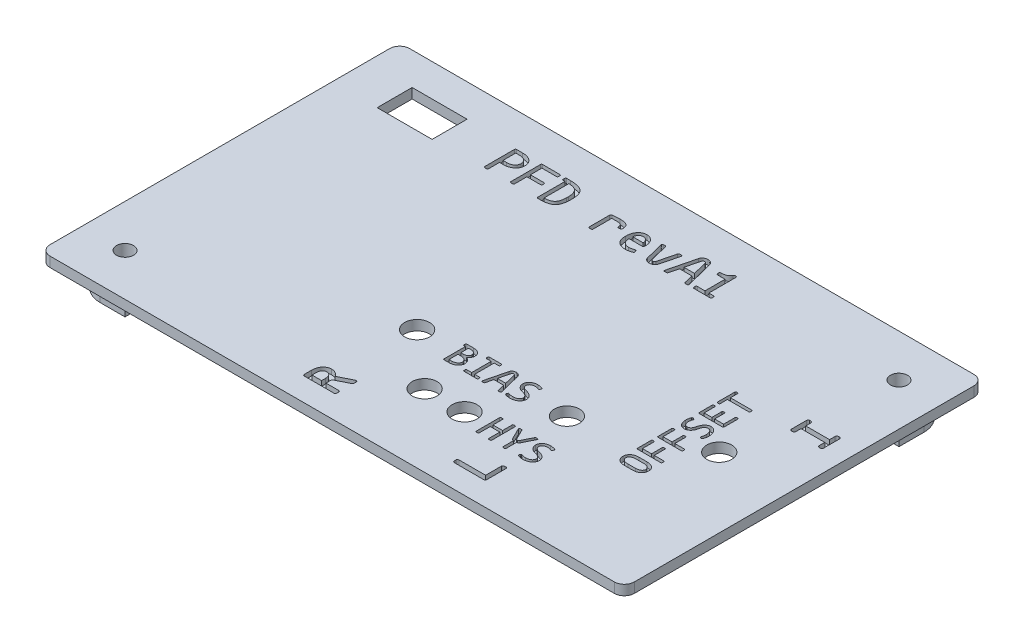
SolidWorks part; units mm, degrees
ref_plane "Front" through (0, 0, 0) normal (0, 0, 1) x (1, 0, 0)
ref_plane "Top" through (0, 0, 0) normal (0, 1, 0) x (1, 0, 0)
ref_plane "Right" through (0, 0, 0) normal (1, 0, 0) x (0, 0, -1)
sketch "Sketch1" plane through (0, 5.45, 0) normal (0, 1, 0) x (1, 0, 0)
  line L1 (-0.502, 5.4133) -> (4.498, 5.4133)
  line L2 (-5.502, 10.4133) -> (-5.502, 15.4133)
  line L3 (-5.502, 15.4133) -> (-0.502, 15.4133)
  line L4 (4.498, 5.4133) -> (4.498, 10.4133)
  line L5 (99.498, 70.4133) -> (94.498, 70.4133)
  line L6 (104.498, 65.4133) -> (104.498, 60.4133)
  line L7 (104.498, 60.4133) -> (99.498, 60.4133)
  line L8 (94.498, 70.4133) -> (94.498, 65.4133)
  arc A0 (99.498, 70.4133) -> (104.498, 65.4133) centre (99.498, 65.4133) cw
  arc A1 (-0.502, 5.4133) -> (-5.502, 10.4133) centre (-0.502, 10.4133) cw
  arc A2 (99.498, 60.4133) -> (94.498, 65.4133) centre (99.498, 65.4133) cw
  arc A3 (-0.502, 15.4133) -> (4.498, 10.4133) centre (-0.502, 10.4133) cw
  point P12 (104.498, 70.4133)
  point P15 (-5.502, 5.4133)
  point P18 (94.498, 60.4133)
  point P21 (4.498, 15.4133)
  dimension "D5" = 5
  dimension "D1" = 10
  dimension "D2" = 10
  dimension "D3" = 10
  dimension "D4" = 10
extrude "Boss-Extrude1" add sketch "Sketch1" along normal up to surface (4.55 mm away)
sketch "Sketch2" plane through (0, 10, 0) normal (0, 1, 0) x (1, 0, 0)
  line L0 (-7.002, 73.9133) -> (105.998, 73.9133) construction
  line L1 (-9.002, 1.9133) -> (107.998, 1.9133)
  line L2 (-9.002, 1.9133) -> (-9.002, 73.9133)
  line L3 (-9.002, 73.9133) -> (107.998, 73.9133)
  line L4 (107.998, 1.9133) -> (107.998, 73.9133)
  line L5 (107.998, 52.9133) -> (107.998, 71.9133) construction
  line L6 (-7.002, 1.9133) -> (37.498, 1.9133) construction
  line L7 (-9.002, 3.9133) -> (-9.002, 71.9133) construction
extrude "Boss-Extrude2" add sketch "Sketch2" along normal blind 2
fillet "Fillet1" radius 2 4 edges at (-9.002, 11, -1.9133) (-9.002, 11, -73.9133) (107.998, 11, -1.9133) (107.998, 11, -73.9133)
sketch "Sketch3" plane through (0, 12, 0) normal (0, 1, 0) x (1, 0, 0)
  line L0 (-7.002, 1.9133) -> (105.998, 1.9133) construction
  line L1 (104.498, 5.4133) -> (-5.502, 5.4133) construction
  line L2 (104.498, 5.4133) -> (104.498, 70.4133) construction
  line L3 (104.498, 70.4133) -> (-5.502, 70.4133) construction
  line L4 (-5.502, 5.4133) -> (-5.502, 70.4133) construction
  line L5 (107.998, 3.9133) -> (107.998, 71.9133) construction
  line L7 (10.998, 60.4133) -> (-0.002, 60.4133)
  line L8 (10.998, 60.4133) -> (10.998, 67.4133)
  line L9 (10.998, 67.4133) -> (-0.002, 67.4133)
  line L10 (-0.002, 60.4133) -> (-0.002, 67.4133)
  circle A0 centre (72.498, 25.9133) radius 2.5
  circle A1 centre (42.498, 25.9133) radius 2.5
  circle A2 centre (53.498, 16.4133) radius 2.5
  circle A3 centre (61.498, 16.4133) radius 2.5
  circle A4 centre (93.998, 34.9133) radius 2.5
  point P4 (49.498, 1.9133)
  point P5 (49.498, 5.4133)
  point P8 (107.998, 37.9133)
  point P9 (104.498, 37.9133)
  point P26 (99.498, 65.4133)
  point P27 (-0.502, 10.4133)
  dimension "D3" = 5
  dimension "D4" = 5
  dimension "D5" = 5
  dimension "D6" = 5
  dimension "D7" = 5
  dimension "D1" = 110
  dimension "D2" = 65
  dimension "D8" = 32
  dimension "D9" = 62
  dimension "D10" = 20.5
  dimension "D11" = 20.5
  dimension "D12" = 43
  dimension "D13" = 51
  dimension "D14" = 11
  dimension "D15" = 11
  dimension "D16" = 29.5
  dimension "D17" = 10.5
  dimension "D18" = 93.5
  dimension "D19" = 55
  dimension "D20" = 62
  dimension "D21" = 104.5
  dimension "D22" = 5
  dimension "D23" = 5
  dimension "D24" = 5
  dimension "D25" = 5
extrude "Cut-Extrude1" cut sketch "Sketch3" against normal up to next
hole_wizard "M3 Clearance Hole1" positions "Sketch5" profile "Sketch7" hole size "M3" standard "ANSI Metric" end condition through all
sketch "Sketch5" plane through (0, 12, 0) normal (0, 1, 0) x (1, 0, 0)
  point P0 (-0.502, 10.4133)
  point P3 (99.498, 65.4133)
sketch "Sketch7" plane through (-0.502, 12, -10.4133) normal (1, 0, 0) x (0, 0, 1)
  line L0 (0, 0) -> (0, 6.55)
  line L1 (0, 6.55) -> (1.7, 6.55)
  line L2 (1.7, 6.55) -> (1.7, 0)
  line L5 (1.7, 0) -> (0, 0)
  line L11 (0, -6.35) -> (0, 107.95) construction
  dimension "Thru Hole Dia." = 3.4
  dimension "Thru Hole Depth" = 6.55
sketch "Sketch10" plane through (0, 12, 0) normal (0, 1, 0) x (1, 0, 0)
  line L0 (90.1307, 22.5157) -> (90.1307, 67.3057) construction
  line L1 (65.5331, 14.065) -> (86.342, 14.065) construction
  line L2 (45.4758, 5.8903) -> (45.4758, 43.9383) construction
  line L3 (75.488, 5.8903) -> (75.488, 51.6069) construction
  line L4 (49.533, 23.3843) -> (65.92, 23.3843) construction
  line L5 (103.7485, 45.0548) -> (103.7485, 56.8257) construction
  line L6 (20.2063, 60.7692) -> (100.8062, 60.7692) construction
  text T0 "<b>R</b>" font "mononoki" height 6.35
  text T1 "<b>L</b>" font "mononoki" height 6.35
  text T2 "HYS" font "mononoki" height 5
  text T3 "BIAS" font "mononoki" height 5
  text T4 "OFFSET" font "mononoki" height 5
  text T5 "<b>I</b>" font "mononoki" height 6.35
  text T6 "PFD revA1" font "mononoki" height 6.35
  point P12 (14.9778, 58.2997)
  point P13 (96.0054, 56.8257)
  point P14 (100.8062, 56.8257)
  point P15 (-6.5312, 48.7085)
  point P16 (-1.8181, 47.3225)
  point P17 (18.4312, 57.5087)
  point P18 (15.7704, 61.6202)
  point P19 (52.8797, 52.6958)
  point P22 (21.3594, 58.4224)
  point P23 (69.2108, 82.7392)
  point P24 (20.3146, 59.4823)
  point P25 (77.524, 84.8994)
  point P28 (17.3942, 59.7376)
  point P29 (45.4758, 55.0932)
  point P30 (20.2063, 60.7692)
extrude "Cut-Extrude2" cut sketch "Sketch10" against normal blind 1
